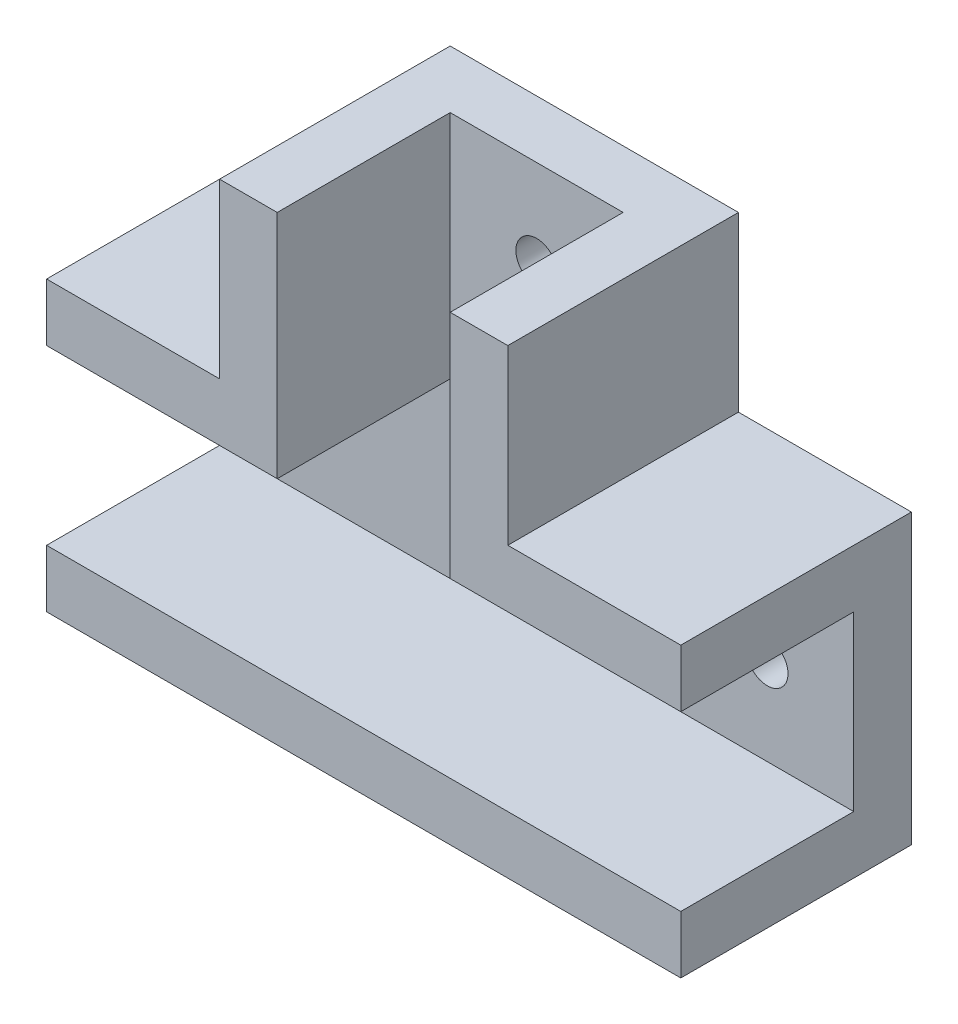
SolidWorks part; units mm, degrees
ref_plane "Front Plane" through (0, 0, 0) normal (0, 0, 1) x (1, 0, 0)
ref_plane "Top Plane" through (0, 0, 0) normal (0, 1, 0) x (1, 0, 0)
ref_plane "Right Plane" through (0, 0, 0) normal (1, 0, 0) x (0, 0, -1)
sketch "Sketch1" plane through (0, 0, 0) normal (0, 0, 1) x (1, 0, 0)
  line L0 (14.3137, -4.2647) -> (34.3137, -4.2647)
  line L1 (-20.6863, -4.2647) -> (-0.6863, -4.2647)
  line L2 (-20.6863, -4.2647) -> (-20.6863, -19.2647)
  line L3 (-20.6863, -19.2647) -> (34.3137, -19.2647)
  line L4 (34.3137, -4.2647) -> (34.3137, -19.2647)
  line L5 (-0.6863, 15.7353) -> (14.3137, 15.7353)
  line L6 (-0.6863, 15.7353) -> (-0.6863, -4.2647)
  line L8 (14.3137, 15.7353) -> (14.3137, -4.2647)
  dimension "D1" = 15
  dimension "D2" = 20
  dimension "D3" = 20
  dimension "D4" = 15
  dimension "D5" = 20
extrude "Boss-Extrude1" add sketch "Sketch1" along normal blind 5
sketch "Sketch2" plane through (0, 0, 0) normal (0, 0, -1) x (-1, 0, 0)
  line L0 (0.6863, 15.7353) -> (5.6863, 15.7353)
  line L1 (5.6863, 15.7353) -> (5.6863, 0.7353)
  line L2 (20.6863, -4.2647) -> (20.6863, 0.7353)
  line L3 (20.6863, 0.7353) -> (6.08, 0.7353)
  line L4 (20.6863, -4.2647) -> (0.6863, -4.2647)
  line L5 (0.6863, 15.7353) -> (0.6863, -4.2647)
  line L6 (6.08, 0.7353) -> (5.6863, 0.7353)
  dimension "D1" = 5
  dimension "D2" = 5
extrude "Boss-Extrude2" add sketch "Sketch2" against normal blind 20 contours L3 L6 L1 L0 L5 L4 L2
sketch "Sketch4" plane through (0, 0, 0) normal (0, 0, -1) x (-1, 0, 0)
  line L0 (20.6863, -19.2647) -> (-34.3137, -19.2647)
  line L1 (-34.3137, -19.2647) -> (-34.3137, -24.2647)
  line L2 (-34.3137, -24.2647) -> (20.6863, -24.2647)
  line L3 (20.6863, -24.2647) -> (20.6863, -19.2647)
  dimension "D1" = 5
extrude "Boss-Extrude3" add sketch "Sketch4" against normal blind 20
ref_plane "Plane4" through (6.8137, 0, 0) normal (-1, 0, 0) x (0, 0, 1)
ref_plane "Plane5" through (-5.6863, 0, 0) normal (-1, 0, 0) x (0, 0, 1)
mirror "Mirror1" about plane through (6.8137, 0, 0) normal (-1, 0, 0) of "Boss-Extrude2"
sketch "Sketch6" plane through (0, 0, 5) normal (0, 0, 1) x (1, 0, 0)
  line L0 (6.8137, 8.25) -> (6.8137, -8.25) construction
  line L1 (-20.6863, -4.2647) -> (-20.6863, -19.2647) construction
  line L2 (-20.6863, -4.2647) -> (-0.6863, -4.2647) construction
  line L3 (34.3137, -4.2647) -> (14.3137, -4.2647) construction
  line L5 (34.3137, -19.2647) -> (34.3137, -4.2647) construction
  line L6 (14.3137, 15.7353) -> (-0.6863, 15.7353) construction
  circle A0 centre (6.8137, 8.2353) radius 1.8
  circle A1 centre (-13.1863, -11.7647) radius 1.8
  circle A2 centre (26.8137, -11.7647) radius 1.8
  dimension "D1" = 3.6
  dimension "D2" = 3.6
  dimension "D3" = 3.6
  dimension "D5" = 7.5
  dimension "D7" = 7.5
  dimension "D8" = 7.5
  dimension "D4" = 7.5
  dimension "D6" = 7.5
ref_plane "Plane6" through (-5.6863, 0.7353, 20) normal (0, -1, 0) x (-1, 0, 0)
extrude "Cut-Extrude3" cut sketch "Sketch6" against normal through all
